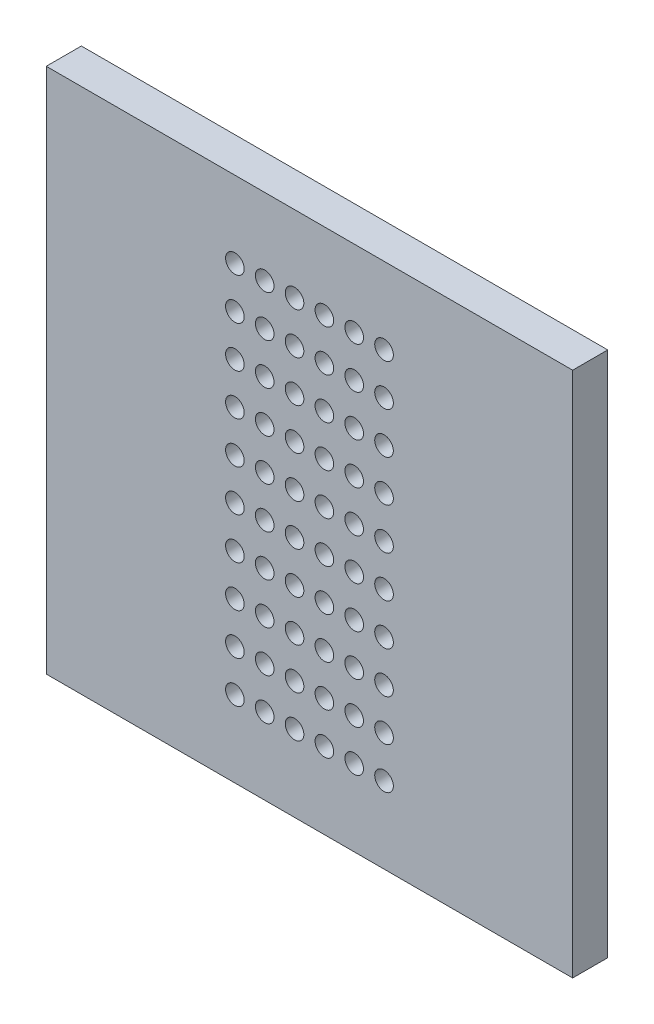
SolidWorks part; units mm, degrees
ref_plane "Plan de face" through (0, 0, 0) normal (0, 0, 1) x (1, 0, 0)
ref_plane "Plan de dessus" through (0, 0, 0) normal (0, 1, 0) x (1, 0, 0)
ref_plane "Plan de droite" through (0, 0, 0) normal (1, 0, 0) x (0, 0, -1)
sketch "Esquisse1" plane through (0, 0, 0) normal (0, 0, 1) x (1, 0, 0)
  line L1 (-15, -15) -> (15, -15)
  line L2 (-15, -15) -> (-15, 15)
  line L3 (-15, 15) -> (15, 15)
  line L4 (15, -15) -> (15, 15)
  line L5 (-15, -15) -> (15, 15) construction
  line L6 (-15, 15) -> (15, -15) construction
  point P0 (0, 0)
extrude "Base_Plate" add sketch "Esquisse1" along normal blind 2
sketch "Sketch_Perforations" plane through (0, 0, 2) normal (0, 0, 1) x (1, 0, 0)
  circle A0 centre (-4.25, -10.64) radius 0.53
  circle A1 centre (-4.25, -8.27) radius 0.53
  circle A2 centre (-4.25, -5.91) radius 0.53
  circle A3 centre (-4.25, -3.55) radius 0.53
  circle A4 centre (-4.25, -1.18) radius 0.53
  circle A5 centre (-4.25, 1.18) radius 0.53
  circle A6 centre (-4.25, 3.55) radius 0.53
  circle A7 centre (-4.25, 5.91) radius 0.53
  circle A8 centre (-4.25, 8.27) radius 0.53
  circle A9 centre (-4.25, 10.64) radius 0.53
  circle A10 centre (-2.55, -10.64) radius 0.53
  circle A11 centre (-2.55, -8.27) radius 0.53
  circle A12 centre (-2.55, -5.91) radius 0.53
  circle A13 centre (-2.55, -3.55) radius 0.53
  circle A14 centre (-2.55, -1.18) radius 0.53
  circle A15 centre (-2.55, 1.18) radius 0.53
  circle A16 centre (-2.55, 3.55) radius 0.53
  circle A17 centre (-2.55, 5.91) radius 0.53
  circle A18 centre (-2.55, 8.27) radius 0.53
  circle A19 centre (-2.55, 10.64) radius 0.53
  circle A20 centre (-0.85, -10.64) radius 0.53
  circle A21 centre (-0.85, -8.27) radius 0.53
  circle A22 centre (-0.85, -5.91) radius 0.53
  circle A23 centre (-0.85, -3.55) radius 0.53
  circle A24 centre (-0.85, -1.18) radius 0.53
  circle A25 centre (-0.85, 1.18) radius 0.53
  circle A26 centre (-0.85, 3.55) radius 0.53
  circle A27 centre (-0.85, 5.91) radius 0.53
  circle A28 centre (-0.85, 8.27) radius 0.53
  circle A29 centre (-0.85, 10.64) radius 0.53
  circle A30 centre (0.85, -10.64) radius 0.53
  circle A31 centre (0.85, -8.27) radius 0.53
  circle A32 centre (0.85, -5.91) radius 0.53
  circle A33 centre (0.85, -3.55) radius 0.53
  circle A34 centre (0.85, -1.18) radius 0.53
  circle A35 centre (0.85, 1.18) radius 0.53
  circle A36 centre (0.85, 3.55) radius 0.53
  circle A37 centre (0.85, 5.91) radius 0.53
  circle A38 centre (0.85, 8.27) radius 0.53
  circle A39 centre (0.85, 10.64) radius 0.53
  circle A40 centre (2.55, -10.64) radius 0.53
  circle A41 centre (2.55, -8.27) radius 0.53
  circle A42 centre (2.55, -5.91) radius 0.53
  circle A43 centre (2.55, -3.55) radius 0.53
  circle A44 centre (2.55, -1.18) radius 0.53
  circle A45 centre (2.55, 1.18) radius 0.53
  circle A46 centre (2.55, 3.55) radius 0.53
  circle A47 centre (2.55, 5.91) radius 0.53
  circle A48 centre (2.55, 8.27) radius 0.53
  circle A49 centre (2.55, 10.64) radius 0.53
  circle A50 centre (4.25, -10.64) radius 0.53
  circle A51 centre (4.25, -8.27) radius 0.53
  circle A52 centre (4.25, -5.91) radius 0.53
  circle A53 centre (4.25, -3.55) radius 0.53
  circle A54 centre (4.25, -1.18) radius 0.53
  circle A55 centre (4.25, 1.18) radius 0.53
  circle A56 centre (4.25, 3.55) radius 0.53
  circle A57 centre (4.25, 5.91) radius 0.53
  circle A58 centre (4.25, 8.27) radius 0.53
  circle A59 centre (4.25, 10.64) radius 0.53
extrude "Cut_Perforations" cut sketch "Sketch_Perforations" against normal blind 10
